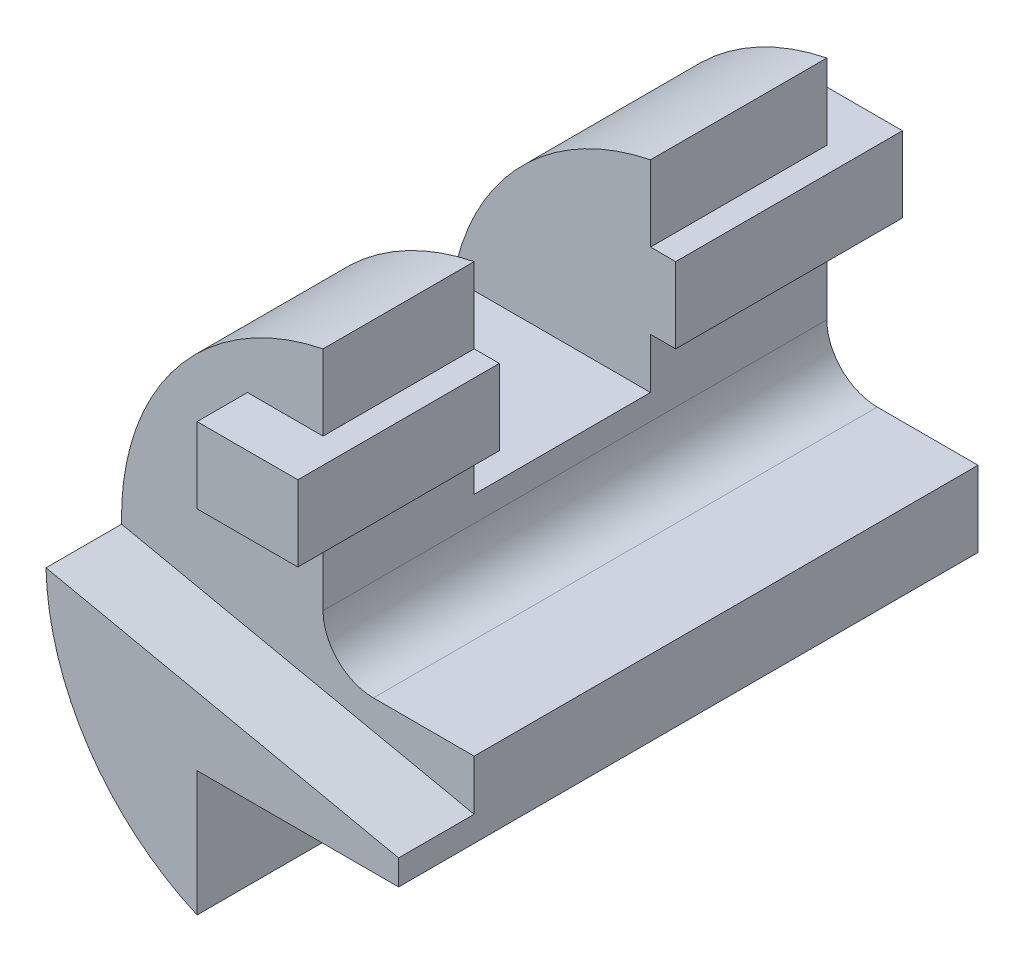
SolidWorks part; units mm, degrees
material "1060 Alloy"
ref_plane "Front Plane" through (0, 0, 0) normal (0, 0, 1) x (1, 0, 0)
ref_plane "Top Plane" through (0, 0, 0) normal (0, 1, 0) x (1, 0, 0)
ref_plane "Right Plane" through (0, 0, 0) normal (1, 0, 0) x (0, 0, -1)
sketch "Sketch1" plane through (0, 0, 0) normal (0, 0, 1) x (1, 0, 0)
  line L0 (-20, -45.8258) -> (-20, -21.0102)
  line L1 (-20, -21.0102) -> (20, -21.0102)
  line L2 (20, -21.0102) -> (20, -6.0102)
  line L3 (20, -6.0102) -> (0, -6.0102)
  line L4 (-10, 3.9898) -> (-10, 48.9898)
  line L5 (0, 25.4519) -> (0, -45.8258) construction
  arc A0 (-10, 48.9898) -> (-20, -45.8258) centre (0, 0) ccw
  arc A1 (0, -6.0102) -> (-10, 3.9898) centre (0, 3.9898) cw
  point P12 (0, -45.8258)
  dimension "D1" = 10
  dimension "D6" = 50
  dimension "D2" = 10
  dimension "D3" = 20
  dimension "D4" = 15
  dimension "D5" = 40
  dimension "D7" = 55
  dimension "D8" = 20
extrude "Boss-Extrude1" add sketch "Sketch1" along normal blind 100
sketch "Sketch2" plane through (-10, 0, 0) normal (1, 0, 0) x (0, 0, -1)
  line L0 (-100, 48.9898) -> (0, 48.9898) construction
  line L1 (-70, 48.9898) -> (-35, 48.9898)
  line L2 (-70, 48.9898) -> (-70, 8.9898)
  line L3 (-70, 8.9898) -> (-35, 8.9898)
  line L4 (-35, 48.9898) -> (-35, 8.9898)
  line L5 (-100, 3.9898) -> (-100, 48.9898) construction
  dimension "D1" = 35
  dimension "D2" = 30
  dimension "D3" = 40
extrude "Cut-Extrude1" cut sketch "Sketch2" against normal up to next
sketch "Sketch3" plane through (0, 0, 35) normal (0, 0, 1) x (1, 0, 0)
  line L0 (-10, 3.9898) -> (-10, 48.9898) construction
  line L1 (-25, 33.9898) -> (-5, 33.9898)
  line L2 (-25, 33.9898) -> (-25, 18.9898)
  line L3 (-25, 18.9898) -> (-5, 18.9898)
  line L4 (-5, 33.9898) -> (-5, 18.9898)
  line L5 (-49.1852, 8.9898) -> (-10, 8.9898) construction
  dimension "D1" = 5
  dimension "D2" = 15
  dimension "D3" = 15
  dimension "D4" = 10
  dimension "D5" = 20
extrude "Boss-Extrude2" add sketch "Sketch3" against normal blind 45
sketch "Sketch4" plane through (0, 0, 70) normal (0, 0, -1) x (-1, 0, 0)
  line L1 (25, 33.9898) -> (5, 33.9898)
  line L2 (25, 33.9898) -> (25, 18.9898)
  line L3 (25, 18.9898) -> (5, 18.9898)
  line L4 (5, 33.9898) -> (5, 18.9898)
extrude "Boss-Extrude3" add sketch "Sketch4" against normal blind 40
sketch "Sketch5" plane through (0, 0, 100) normal (0, 0, 1) x (1, 0, 0)
  line L0 (20, -16.0102) -> (-49.9871, -1.134)
  line L1 (20, -21.0102) -> (20, -6.0102) construction
  line L2 (-20, -21.0102) -> (20, -21.0102) construction
  line L3 (20, -16.0102) -> (20, -21.0102)
  line L4 (-20, -45.8258) -> (-20, -21.0102) construction
  line L5 (-20, -45.8258) -> (-20, -21.0102)
  line L6 (-20, -21.0102) -> (20, -21.0102)
  arc A0 (-10, 48.9898) -> (-20, -45.8258) centre (0, 0) ccw construction
  arc A1 (-49.9871, -1.134) -> (-20, -45.8258) centre (0, 0) ccw
  dimension "D1" = 78
  dimension "D2" = 5
extrude "Boss-Extrude4" add sketch "Sketch5" along normal blind 15
equation "\"A\"= 50"
equation "\"B\"= 55"
equation "\"C\"= 35"
equation "\"D6@Sketch1\"=\"A\""
equation "\"D7@Sketch1\"=\"B\""
equation "\"D1@Sketch2\"=\"C\""
